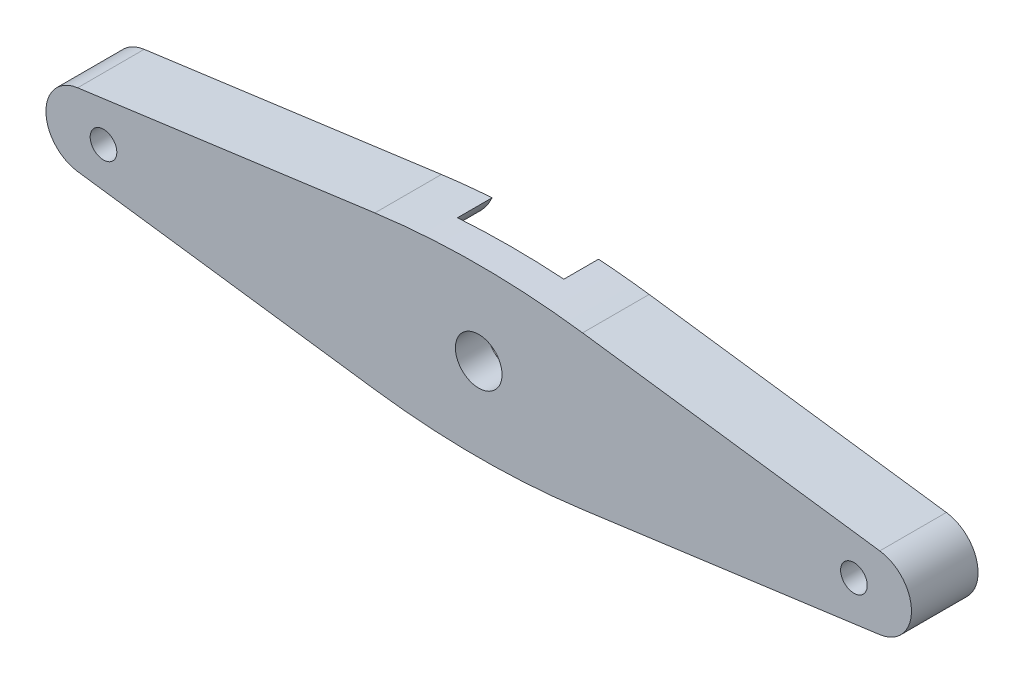
SolidWorks part; units mm, degrees
ref_plane "Piano frontale" through (0, 0, 0) normal (0, 0, 1) x (1, 0, 0)
ref_plane "Piano superiore" through (0, 0, 0) normal (0, 1, 0) x (1, 0, 0)
ref_plane "Piano destro" through (0, 0, 0) normal (1, 0, 0) x (0, 0, -1)
sketch "Schizzo1" plane through (0, 0, 0) normal (0, 0, 1) x (1, 0, 0)
  line L0 (254.7947, 1025.8045) -> (1132.8538, 959.1253) construction
  line L1 (0, 0) -> (36, 0) construction
  line L3 (24.9484, 3.7343) -> (24.9484, -3.7657) construction
  line L4 (24.9484, 3.7343) -> (34.6084, 1.7129)
  line L12 (24.9484, -3.7343) -> (34.6084, -1.7129)
  line L13 (21.7343, -6.9484) -> (19.7129, -16.6084)
  line L14 (14.2657, -6.9484) -> (16.2871, -16.6084)
  line L15 (11.0516, -3.7343) -> (1.3916, -1.7129)
  line L16 (11.0516, 3.7343) -> (1.3916, 1.7129)
  line L17 (14.2657, 6.9484) -> (16.2871, 16.6084)
  line L18 (21.7343, 6.9484) -> (19.7129, 16.6084)
  line L19 (24.9484, 3.7343) -> (11.0516, 3.7343) construction
  circle A16 centre (18, 0) radius 1.75
  arc A18 (34.6084, -1.7129) -> (34.6084, 1.7129) centre (34.25, 0) ccw
  arc A21 (16.2871, -16.6084) -> (19.7129, -16.6084) centre (18, -16.25) ccw
  arc A22 (1.3916, 1.7129) -> (1.3916, -1.7129) centre (1.75, 0) ccw
  arc A23 (19.7129, 16.6084) -> (16.2871, 16.6084) centre (18, 16.25) ccw
  arc A24 (14.2657, -6.9484) -> (11.0516, -3.7343) centre (10.201, -7.799) ccw
  arc A25 (11.0516, 3.7343) -> (14.2657, 6.9484) centre (10.201, 7.799) ccw
  arc A26 (21.7343, 6.9484) -> (24.9484, 3.7343) centre (25.799, 7.799) ccw
  arc A27 (24.9484, -3.7343) -> (21.7343, -6.9484) centre (25.799, -7.799) ccw
  dimension "D1" = 36
  dimension "D2" = 3.5
  dimension "D4" = 3.5
  dimension "D7" = 4
  dimension "D3" = 7.5
  dimension "D5" = 9.66
  dimension "D6" = 4
sketch "Schizzo5" plane through (0, 0, 0) normal (0, 0, 1) x (1, 0, 0)
  line L0 (-14.5, 0) -> (50.5, 0) construction
  line L1 (-12.1187, -2.7252) -> (10.1996, -5.7447)
  line L2 (48.1187, 2.7252) -> (25.8004, 5.7447)
  line L3 (-12.1187, 2.7252) -> (10.1996, 5.7447)
  line L4 (48.1187, -2.7252) -> (25.8004, -5.7447)
  circle A0 centre (18, 0) radius 1.75 construction
  circle A1 centre (18, 0) radius 1.75
  arc A2 (-12.1187, 2.7252) -> (-12.1187, -2.7252) centre (-11.75, 0) ccw
  arc A3 (48.1187, -2.7252) -> (48.1187, 2.7252) centre (47.75, 0) ccw
  arc A4 (10.1996, 5.7447) -> (25.8004, 5.7447) centre (18, -51.9098) cw
  arc A5 (10.1996, -5.7447) -> (25.8004, -5.7447) centre (18, 51.9098) ccw
  point P8 (18, 0)
  dimension "D2" = 5.5
  dimension "D1" = 65
  dimension "D3" = 2
extrude "Estrusione-Estrusione3" add sketch "Schizzo5" along normal blind 5
extrude "Taglio-Estrusione3" cut sketch "Schizzo1" along normal blind 2.6
sketch "Schizzo6" plane through (0, 0, 5) normal (0, 0, 1) x (1, 0, 0)
  line L0 (18, 0) -> (18, 9.4482) construction
  circle A0 centre (-10.177, 0) radius 1
  circle A1 centre (46.177, 0) radius 1
  point P5 (46.177, 0)
  dimension "D1" = 2
extrude "Taglio-Estrusione4" cut sketch "Schizzo6" against normal blind 10
